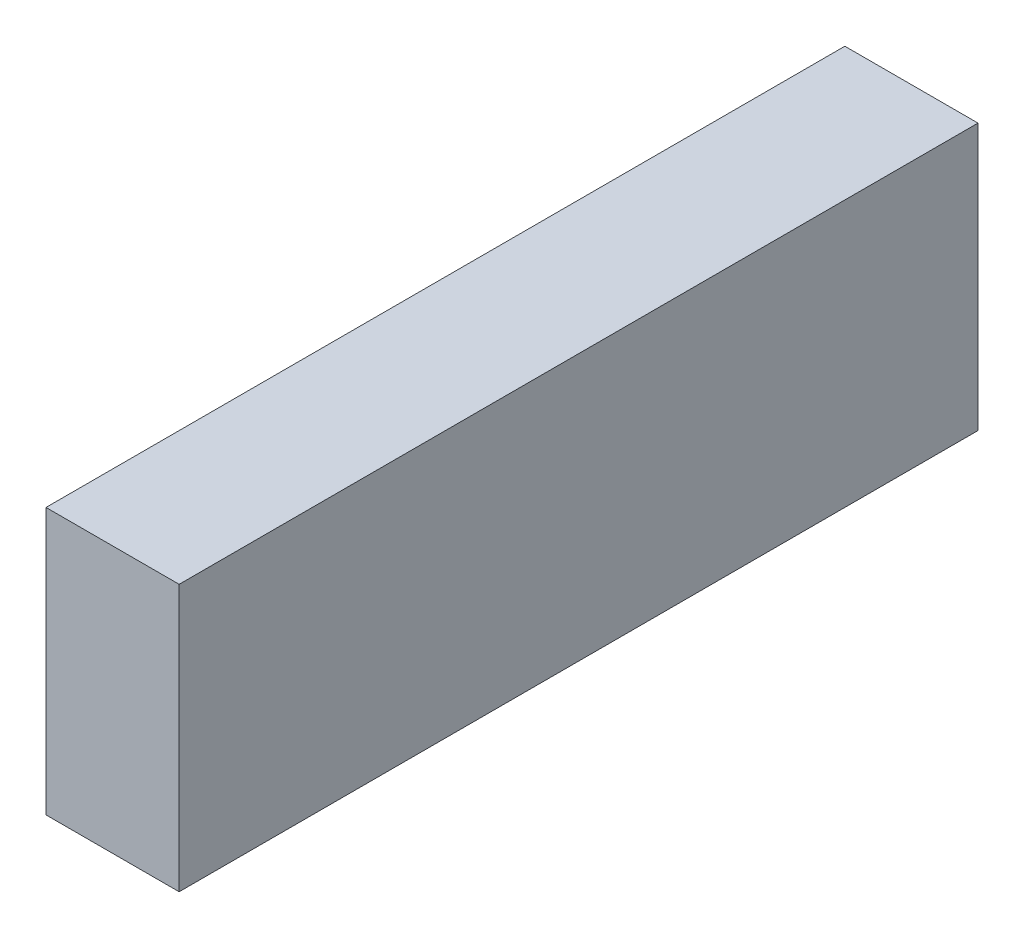
SolidWorks part; units mm, degrees
ref_plane "Front Plane" through (0, 0, 0) normal (0, 0, 1) x (1, 0, 0)
ref_plane "Top Plane" through (0, 0, 0) normal (0, 1, 0) x (1, 0, 0)
ref_plane "Right Plane" through (0, 0, 0) normal (1, 0, 0) x (0, 0, -1)
sketch "Sketch2" plane through (0, 0, 0) normal (1, 0, 0) x (0, 0, -1)
  line L3 (-262.7936, 0) -> (0, 0)
  line L4 (0, 0) -> (139.7, 0)
  line L6 (139.7, 0) -> (139.7, 81.9)
  line L7 (139.7, 81.9) -> (124.7, 81.9)
  line L8 (124.7, 81.9) -> (124.7, 20)
  line L9 (124.7, 20) -> (0, 20)
  line L10 (0, 20) -> (0, 133.7)
  line L11 (0, 133.7) -> (-115, 133.7)
  line L12 (-115, 133.7) -> (-171.1938, 94.3527)
  line L13 (-171.1938, 94.3527) -> (-262.7936, 81.4791)
  line L18 (-262.7936, 81.4791) -> (-262.7936, 31.4791)
  line L19 (-262.7936, 31.4791) -> (-262.7936, 0) construction
  arc A2 (-262.7936, 31.4791) -> (-262.7936, 0) centre (-255.1441, 15.7396) ccw
  dimension "D12" = 17.5
  dimension "D2" = 113.7
  dimension "D3" = 20
  dimension "D4" = 35
  dimension "D5" = 153
  dimension "D6" = 139.7
  dimension "D7" = 15
  dimension "D8" = 61.9
  dimension "D9" = 92.5
  dimension "D10" = 68.6
  dimension "D11" = 50
  dimension "D13" = 115
extrude "Boss-Extrude1" add sketch "Sketch2" along normal mid plane 138
sketch "Sketch4" plane through (0, 20, 0) normal (0, 1, 0) x (1, 0, 0)
  line L0 (69, 124.7) -> (-69, 124.7) construction
  line L1 (69, 0) -> (54, 0)
  line L2 (69, 0) -> (69, 124.7)
  line L3 (69, 124.7) -> (54, 124.7)
  line L4 (54, 0) -> (54, 124.7)
  dimension "D1" = 15
extrude "Boss-Extrude2" add sketch "Sketch4" along normal up to surface (61.9 mm away) up to face at (0, 81.9, -132.2)
mirror "Mirror1" about plane through (0, 0, 0) normal (1, 0, 0) of "Boss-Extrude2"
sketch "Sketch5" plane through (69, 0, 0) normal (1, 0, 0) x (0, 0, -1)
  line L0 (-262.7936, 0) -> (139.7, 0) construction
  line L1 (-224.9441, 0) -> (-160.3441, 0)
  line L2 (28.0559, 0) -> (92.6559, 0)
  arc A0 (-224.9441, 0) -> (-160.3441, 0) centre (-192.6441, 0) ccw
  arc A1 (28.0559, 0) -> (92.6559, 0) centre (60.3559, 0) ccw
  arc A2 (-262.7936, 31.4791) -> (-262.7936, 0) centre (-255.1441, 15.7396) ccw construction
  point P11 (-272.6441, 15.7396)
  dimension "D3" = 32.3
  dimension "D1" = 333
  dimension "D2" = 80
extrude "Boss-Extrude3" add sketch "Sketch5" against normal blind 20.4
mirror "Mirror2" about plane through (0, 0, 0) normal (1, 0, 0) of "Boss-Extrude3"
fillet "Fillet1" radius 10 5 edges at (0, 133.7, 0) (0, 133.7, 115) (0, 94.3527, 171.1938) (0, 81.4791, 262.7936) (0, 31.4791, 262.7936)
sketch "Sketch6" plane through (0, 0, 0) normal (1, 0, 0) x (0, 0, -1)
  line L0 (-192.6441, 0) -> (-192.6441, -32.3) construction
  line L1 (-2192.6441, -32.3) -> (3807.3559, -32.3)
  line L2 (-2192.6441, -32.3) -> (-2192.6441, 1967.7)
  line L3 (-2192.6441, 1967.7) -> (3807.3559, 1967.7)
  line L4 (3807.3559, -32.3) -> (3807.3559, 1967.7)
  arc A0 (-224.9441, 0) -> (-160.3441, 0) centre (-192.6441, 0) ccw construction
  dimension "D1" = 2000
  dimension "D2" = 6000
  dimension "D3" = 2000
extrude "Boss-Extrude4" add sketch "Sketch6" along normal blind 1000 separate body
sketch "Sketch8" plane through (0, 0, 0) normal (1, 0, 0) x (0, 0, -1)
  line L1 (-392.6441, -32.3) -> (487.3559, -32.3)
  line L2 (-392.6441, -32.3) -> (-392.6441, 407.7)
  line L3 (-392.6441, 407.7) -> (487.3559, 407.7)
  line L4 (487.3559, -32.3) -> (487.3559, 407.7)
  arc A0 (-224.9441, 0) -> (-160.3441, 0) centre (-192.6441, 0) ccw construction
  point P7 (-192.6441, -32.3)
  dimension "D1" = 880
  dimension "D2" = 440
  dimension "D3" = 200
extrude "Boss-Extrude5" add sketch "Sketch8" along normal blind 220 separate body
